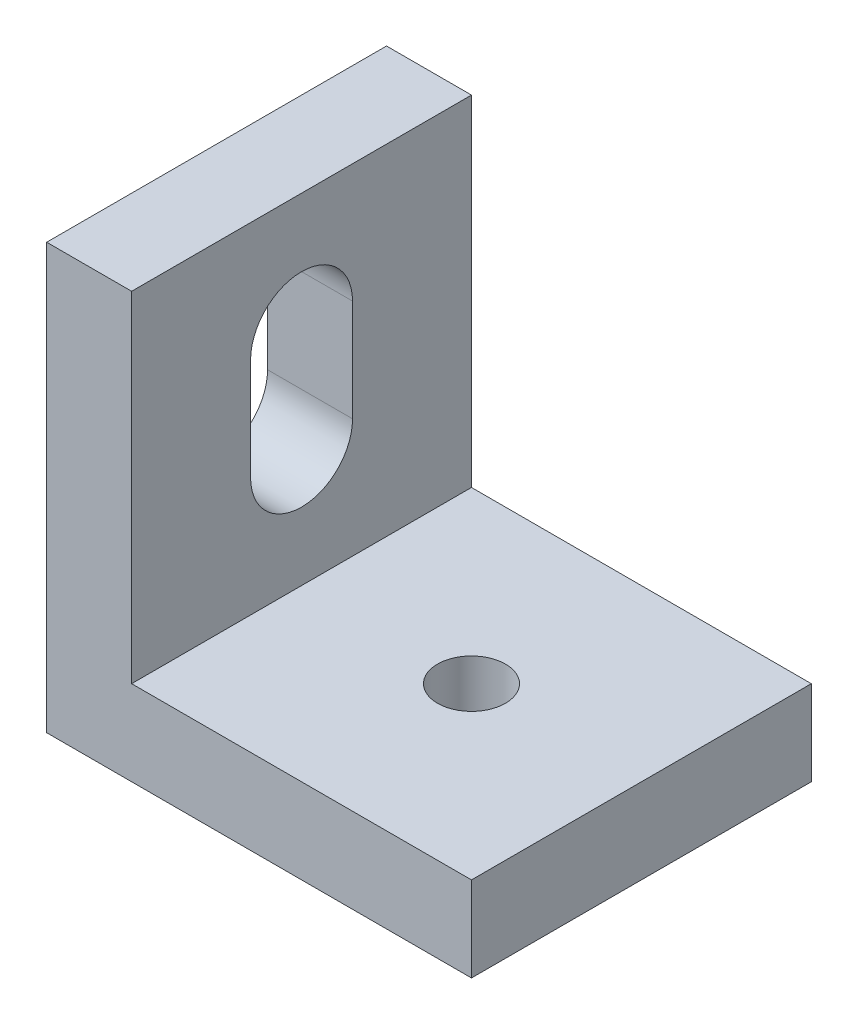
SolidWorks part; units mm, degrees
ref_plane "Front Plane" through (0, 0, 0) normal (0, 0, 1) x (1, 0, 0)
ref_plane "Top Plane" through (0, 0, 0) normal (0, 1, 0) x (1, 0, 0)
ref_plane "Right Plane" through (0, 0, 0) normal (1, 0, 0) x (0, 0, -1)
sketch "Sketch1" plane through (0, 0, 0) normal (0, 1, 0) x (1, 0, 0)
  line L1 (-10, 10) -> (10, 10)
  line L2 (-10, 10) -> (-10, -10)
  line L3 (-10, -10) -> (10, -10)
  line L4 (10, 10) -> (10, -10)
  line L5 (-10, 10) -> (10, -10) construction
  line L6 (-10, -10) -> (10, 10) construction
  circle A0 centre (0, 0) radius 2
  point P0 (0, 0)
  dimension "D2" = 4
  dimension "D1" = 20
extrude "Boss-Extrude1" add sketch "Sketch1" along normal blind 5
sketch "Sketch2" plane through (0, 0, 0) normal (0, -1, 0) x (1, 0, 0)
  line L0 (-10, 10) -> (-10, -10)
  line L1 (-10, 10) -> (-15, 10)
  line L2 (-10, -10) -> (-15, -10)
  line L3 (-15, 10) -> (-15, -10)
  dimension "D1" = 5
extrude "Boss-Extrude2" add sketch "Sketch2" against normal blind 25
sketch "Sketch3" plane through (-10, 0, 0) normal (1, 0, 0) x (0, 0, -1)
  line L0 (0, 0) -> (0, 25) construction
  line L1 (10, 25) -> (-10, 25) construction
  line L2 (-10, 5) -> (10, 5) construction
  line L4 (-3, 18) -> (3, 18)
  line L5 (-3, 18) -> (-3, 12)
  line L6 (-3, 12) -> (3, 12)
  line L7 (3, 18) -> (3, 12)
  line L8 (-3, 18) -> (3, 12) construction
  line L9 (-3, 12) -> (3, 18) construction
  arc A0 (-3, 18) -> (3, 18) centre (0, 18) cw
  arc A1 (3, 12) -> (-3, 12) centre (0, 12) cw
  point P5 (0, 5)
  point P6 (0, 15)
  dimension "D1" = 10
  dimension "D2" = 6
  dimension "D3" = 6
extrude "Cut-Extrude1" cut sketch "Sketch3" against normal blind 25 contours A0 L4 | L7 L4 L5 L6 | A1 L6
